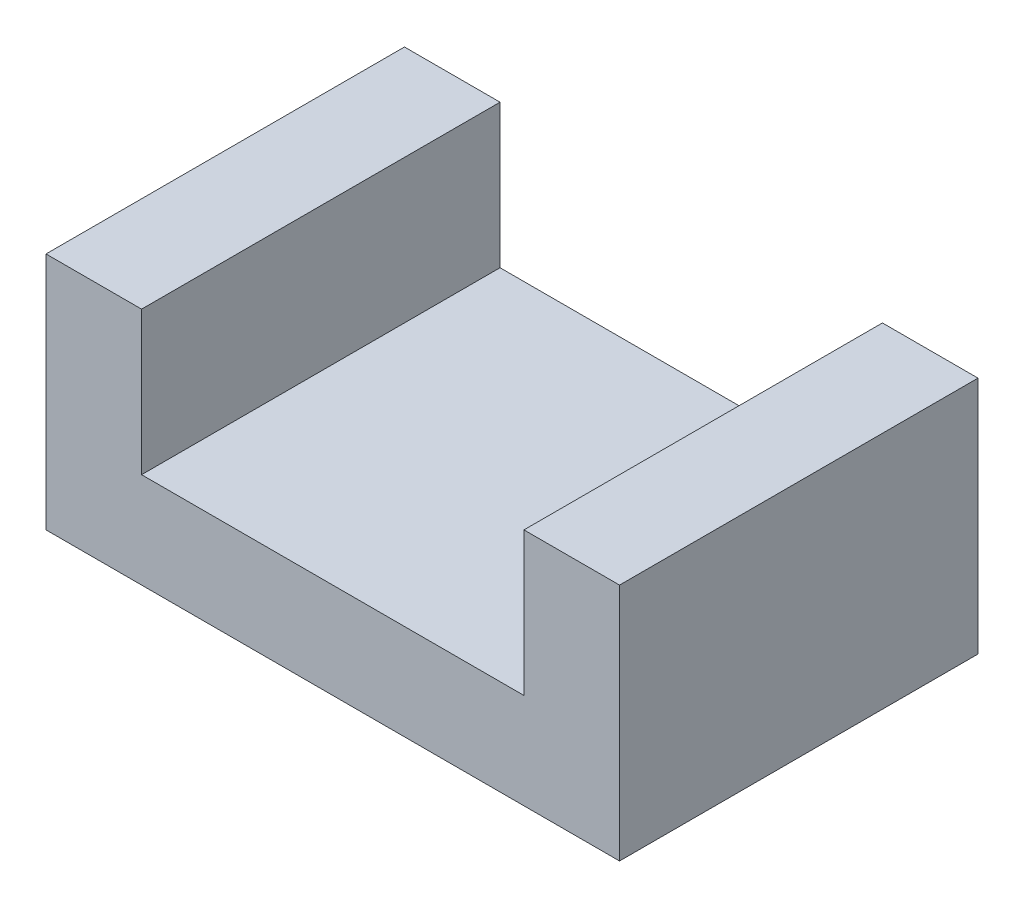
SolidWorks part; units mm, degrees
ref_plane "Front Plane" through (0, 0, 0) normal (0, 0, 1) x (1, 0, 0)
ref_plane "Top Plane" through (0, 0, 0) normal (0, 1, 0) x (1, 0, 0)
ref_plane "Right Plane" through (0, 0, 0) normal (1, 0, 0) x (0, 0, -1)
sketch "Sketch1" plane through (0, 0, 0) normal (0, 1, 0) x (1, 0, 0)
  line L1 (0, 0) -> (24, 0)
  line L2 (0, 0) -> (0, 15)
  line L3 (0, 15) -> (24, 15)
  line L4 (24, 0) -> (24, 15)
  dimension "D1" = 24
  dimension "D2" = 15
extrude "Boss-Extrude1" add sketch "Sketch1" along normal blind 4
sketch "Sketch2" plane through (0, 4, 0) normal (0, 1, 0) x (1, 0, 0)
  line L0 (4, 15) -> (4, 0)
  line L1 (24, 15) -> (0, 15) construction
  line L2 (0, 0) -> (24, 0) construction
  line L3 (0, 15) -> (0, 0) construction
  line L4 (20, 15) -> (20, 0)
  line L5 (24, 0) -> (24, 15) construction
  line L6 (4, 15) -> (0, 15)
  line L7 (0, 15) -> (0, 0)
  line L8 (0, 0) -> (4, 0)
  line L9 (20, 15) -> (24, 15)
  line L10 (24, 15) -> (24, 0)
  line L11 (24, 0) -> (20, 0)
  dimension "D1" = 4
  dimension "D2" = 4
extrude "Boss-Extrude2" add sketch "Sketch2" along normal blind 6
